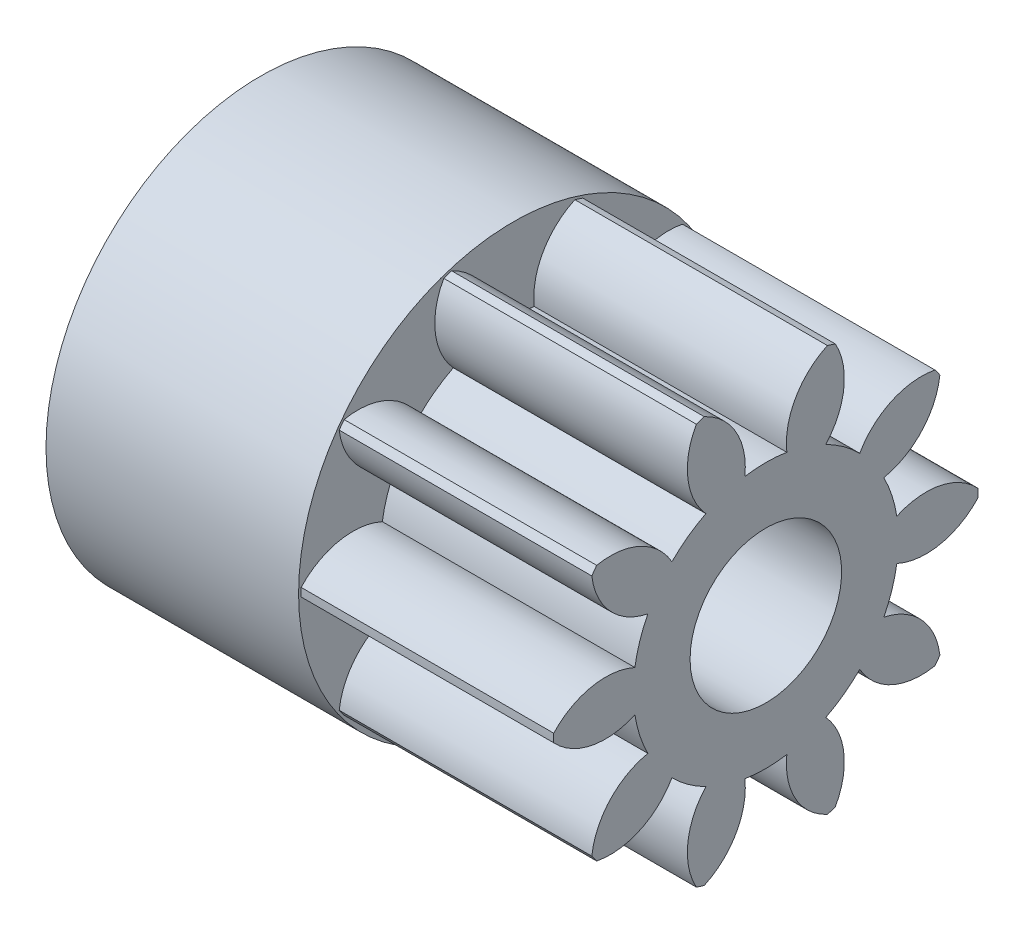
SolidWorks part; units mm, degrees
ref_plane "Plane1" through (0, 0, 0) normal (0, 0, 1) x (1, 0, 0)
ref_plane "Plane2" through (0, 0, 0) normal (0, 1, 0) x (1, 0, 0)
ref_plane "Plane3" through (0, 0, 0) normal (1, 0, 0) x (0, 0, -1)
sketch "HoldingSke" plane through (0, 0, 0) normal (0, 1, 0) x (1, 0, 0)
  line L0 (0, 0) -> (1.4069, -0.2481)
  line L1 (-15, 0) -> (100, 0) construction
  line L2 (0, 0) -> (-2.1039, 2.3779)
  line L3 (0, 0) -> (-11.863, 4.5341)
  line L4 (0, 0) -> (8.5048, 1.4996)
  line L5 (0, 0) -> (-46.8476, -17.4728)
  line L6 (0, 0) -> (-4.1448, -2.7965)
  line L7 (-2.1039, 2.3779) -> (8.6586, 51.2059)
  line L8 (-76.2, 54.61) -> (-75.7, 54.61)
  line L9 (-71.009, 38.7566) -> (-53.1078, 45.2721)
  line L10 (-76.2, 71.12) -> (104.1128, 71.12)
  line L11 (0, 0) -> (-5, 0)
  line L12 (-76.2, 101.6) -> (-76.173, 101.6)
  line L13 (24.9733, 27.94) -> (52.9518, 28.4284)
  line L14 (24.9733, 27.94) -> (24.9743, 27.94)
  line L15 (24.9733, 27.94) -> (100.4006, 29.5858)
  line L16 (-63.627, -0.7) -> (-12.827, -0.7)
  circle A0 centre (0, 0) radius 1.5
  circle A1 centre (0, 0) radius 2.624
  circle A2 centre (0, 0) radius 37.5
  circle A3 centre (0, 0) radius 1.5
  dimension "MHD" = 5.248
  dimension "Hub_dia" = 75
  dimension "Bore" = 3
  dimension "MBD" = 3
  dimension "Num_teeth" = 10
  dimension "Pitch" = 1.4286
  dimension "Overall_len" = 50
  dimension "Show_teeth" = 10
  dimension "Thickness" = 5
  dimension "OAL" = 50.0001
  dimension "T_dim" = 0.5
  dimension "Ap" = 20
  dimension "H" = 19.05
  dimension "Pitch_radius" = 180.3128
  dimension "Width" = 5
  dimension "Backlash" = 0.027
  dimension "Addendum_fac" = 1
  dimension "Dedendum_fac" = 1.25
  dimension "Clearance_fac" = 0.25
  dimension "Dedendum_add" = 0.001
  dimension "Module" = 0.7
sketch "BasProSke" plane through (0, 0, 0) normal (0, 1, 0) x (1, 0, 0)
  line L0 (-10, 0) -> (60, 0) construction
  line L1 (0, 0) -> (0, 4.2)
  line L2 (0, 0) -> (5, 0)
  line L3 (5, 0) -> (5, 4.2)
  line L4 (5, 4.2) -> (0, 4.2)
  dimension "Thickness" = 5
  dimension "Diameter" = 8.4
revolve "Base-Revolve" add sketch "BasProSke" angle 360 about L0
sketch "TooCutSke" plane through (0, 0, 0) normal (1, 0, 0) x (0, 0, -1)
  line L1 (0, 0) -> (0, 107) construction
  line L2 (0, 0) -> (-0.5947, 3.4491) construction
  line L3 (0, 0) -> (-2.1409, 6.589) construction
  line L4 (-0.5947, 3.4491) -> (-1.0705, 3.2945) construction
  arc A0 (0.4155, 2.5909) -> (-0.4155, 2.5909) centre (0, 0) ccw
  arc A1 (1.2546, 4.0349) -> (-1.2546, 4.0349) centre (0, 0) ccw
  circle A2 centre (0, 0) radius 3.5 construction
  circle A3 centre (0, 0) radius 3.2889 construction
  arc A4 (-0.4155, 2.5909) -> (-1.2546, 4.0349) centre (-1.8066, 2.7483) ccw
  arc A5 (1.2546, 4.0349) -> (0.4155, 2.5909) centre (1.8066, 2.7483) ccw
  dimension "Root_dia" = 5.248
  dimension "Overcut_dia" = 8.4508
  dimension "Pitch_dia" = 7
  dimension "Base_dia" = 6.5778
  dimension "Flank_rad" = 1.4
  dimension "Half_ang" = 18
  dimension "Half_CT" = 0.5003
extrude "ToothCut" cut sketch "TooCutSke" along normal through all
fillet "Breaks" [suppressed] radius 0.014
fillet "RootFillets" [suppressed] radius 0.176
pattern_circular "TeethCuts" count 10 every 36 about axis through (-10, 0, 0) along (1, 0, 0) of "ToothCut", "RootFillets", "Breaks"
sketch "HubNeaOneSke" plane through (0, 0, 0) normal (-1, 0, 0) x (0, 0, 1)
  circle A0 centre (0, 0) radius 2.624
  dimension "Diameter" = 5.248
extrude "HubNearOne" [suppressed] add sketch "HubNeaOneSke" along normal blind 45.0001
sketch "HubNeaBotSke" plane through (0, 0, 0) normal (-1, 0, 0) x (0, 0, 1)
  circle A0 centre (0, 0) radius 2.624
  dimension "Diameter" = 5.248
extrude "HubNearBoth" [suppressed] add sketch "HubNeaBotSke" along normal blind 22.5
ref_plane "FarPln" through (5, 0, 0) normal (1, 0, 0) x (0, 0, -1)
sketch "HubFarSke" plane through (5, 0, 0) normal (1, 0, 0) x (0, 0, -1)
  circle A0 centre (0, 0) radius 2.624
  dimension "Diameter" = 5.248
extrude "HubFar" [suppressed] add sketch "HubFarSke" along normal blind 22.5
sketch "BorSke" plane through (0, 0, 0) normal (1, 0, 0) x (0, 0, -1)
  circle A0 centre (0, 0) radius 1.5
  dimension "Diameter" = 3
extrude "Bore" cut sketch "BorSke" along normal mid plane 100.0001
sketch "KeySke" plane through (0, 0, 0) normal (1, 0, 0) x (0, 0, -1)
  line L0 (-0.6, 0) -> (-0.6, 2)
  line L1 (-0.6, 2) -> (0.6, 2)
  line L2 (0.6, 2) -> (0.6, 0)
  line L3 (0, 0) -> (0, 34) construction
  line L4 (-0.6, 0) -> (0.6, 0)
  dimension "Offset" = 2
  dimension "Width" = 1.2
extrude "Keyway" [suppressed] cut sketch "KeySke" along normal mid plane 100.0001
pattern_circular "Keyway2" [suppressed] count 2 every 90 about axis through (-10, 0, 0) along (1, 0, 0)
sketch "Croquis1" plane through (0, 0, 0) normal (-1, 0, 0) x (0, 0, 1)
  circle A0 centre (0, 0) radius 4.25
  circle A1 centre (0, 0) radius 3.25
  dimension "D1" = 8.5
  dimension "D2" = 6.5
extrude "Saliente-Extruir1" add sketch "Croquis1" along normal blind 5
sketch "Croquis2" plane through (0, 0, 0) normal (-1, 0, 0) x (0, 0, 1)
  circle A0 centre (0, 0) radius 3.25
  circle A1 centre (0, 0) radius 3.25 construction
extrude "Saliente-Extruir2" add sketch "Croquis2" along normal blind 2
sketch "Croquis3" plane through (-2, 0, 0) normal (-1, 0, 0) x (0, 0, 1)
  line L0 (-1.5, 2.8831) -> (-1.5, -2.8831)
  circle A0 centre (0, 0) radius 3.25 construction
  circle A1 centre (0, 0) radius 3.25 construction
  arc A2 (-1.5, 2.8831) -> (-1.5, -2.8831) centre (0, 0) ccw
  dimension "D1" = 1.5
extrude "Saliente-Extruir3" add sketch "Croquis3" along normal blind 2
equation "' \"Module@HoldingSke\" = 6.35"
equation "' \"Num_teeth@HoldingSke\" = 12"
equation "' \"Ap@HoldingSke\" =  20"
equation "' \"Ap@HoldingSke\" = 20"
equation "' \"Width@HoldingSke\" = 0.5 * 25.4"
equation "' \"Hub_dia@HoldingSke\"= 1 * 25.4"
equation "' \"Hub_dia@HoldingSke\" = 1 * 25.4"
equation "' \"Overall_len@HoldingSke\" = 1.0 * 25.4"
equation "' \"Bore@HoldingSke\" = 0.75 * 25.4"
equation "' \"T_dim@HoldingSke\" = 0.1 * 25.4"
equation "' \"Width@KeySke\" = 0.25 * 25.4"
equation "' \"Show_teeth@HoldingSke\" = 13"
equation "' \"Backlash@HoldingSke\" = 0.009 * 25.4"
equation "' \"Addendum_fac@HoldingSke\" = 1.0"
equation "' \"Dedendum_fac@HoldingSke\" = 1.25"
equation "' \"Dedendum_add@HoldingSke\" = 0.00005 * 25.4"
equation "' \"Clearance_fac@HoldingSke\" = 0.25"
equation "\"Pitch@HoldingSke\" = 1 / \"Module@HoldingSke\""
equation "\"Overcut_dia@TooCutSke\" = (\"Num_teeth@HoldingSke\" + 2 * \"Addendum_fac@HoldingSke\") / \"Pitch@HoldingSke\" + 0.002 * 25.4"
equation "\"Pitch_dia@TooCutSke\" = \"Num_teeth@HoldingSke\" / \"Pitch@HoldingSke\""
equation "\"Base_dia@TooCutSke\" = \"Num_teeth@HoldingSke\" / \"Pitch@HoldingSke\" * cos((\"Ap@HoldingSke\"  * 3.14159265 / 180))"
equation "\"Root_dia@TooCutSke\" = (\"Num_teeth@HoldingSke\" + 2) / \"Pitch@HoldingSke\" - 2 * (\"Addendum_fac@HoldingSke\" + \"Dedendum_fac@HoldingSke\") / \"Pitch@HoldingSke\" - \"Dedendum_add@HoldingSke\" * 2"
equation "\"Half_ang@TooCutSke\" = 180 / \"Num_teeth@HoldingSke\""
equation "\"Half_CT@TooCutSke\" = \"Num_teeth@HoldingSke\" / \"Pitch@HoldingSke\" * sin((3.14159265 / 2 / \"Num_teeth@HoldingSke\")) / 2 - 7 * \"Backlash@HoldingSke\" / 4"
equation "\"Flank_rad@TooCutSke\" = \"Num_teeth@HoldingSke\" / \"Pitch@HoldingSke\" / 5"
equation "\"Radius@RootFillets\" = \"Clearance_fac@HoldingSke\" / \"Pitch@HoldingSke\" + \"Dedendum_add@HoldingSke\""
equation "\"Break_rad@Breaks\" = 0.02 / \"Pitch@HoldingSke\""
equation "\"Thickness@HoldingSke\" = \"Width@HoldingSke\""
equation "\"OAL@HoldingSke\" = \"Thickness@HoldingSke\""
equation "\"MHD@HoldingSke\" = (\"Num_teeth@HoldingSke\" + 2) / \"Pitch@HoldingSke\" - 2 * (\"Addendum_fac@HoldingSke\" + \"Dedendum_fac@HoldingSke\")  / \"Pitch@HoldingSke\" - \"Dedendum_add@HoldingSke\" * 2"
equation "\"MBD@HoldingSke\" = (\"Num_teeth@HoldingSke\" + 2) / \"Pitch@HoldingSke\" - 2 * (\"Addendum_fac@HoldingSke\" + \"Dedendum_fac@HoldingSke\")  / \"Pitch@HoldingSke\" - \"Dedendum_add@HoldingSke\" * 2 - 0.002 * 25.4"
equation "\"MHD@HoldingSke\" = ((sgn( \"MHD@HoldingSke\" - \"Hub_dia@HoldingSke\" )-1)*( \"MHD@HoldingSke\" - \"Hub_dia@HoldingSke\" ))/-2+ \"Hub_dia@HoldingSke\""
equation "\"MBD@HoldingSke\" = ((sgn( \"MBD@HoldingSke\" - \"Bore@HoldingSke\" )-1)*( \"MBD@HoldingSke\" - \"Bore@HoldingSke\" ))/-2+ \"Bore@HoldingSke\""
equation "\"OAL@HoldingSke\" = ((sgn( \"OAL@HoldingSke\" - \"Overall_len@HoldingSke\" )+1)*( \"OAL@HoldingSke\" - \"Overall_len@HoldingSke\" ))/2 + \"Overall_len@HoldingSke\" + 0.000002 * 25.4"
equation "\"Num_teeth@TeethCuts\" = int( \"Show_teeth@HoldingSke\" ) + 1"
equation "\"Num_teeth@TeethCuts\" = ((sgn( \"Num_teeth@TeethCuts\" - \"Num_teeth@HoldingSke\" )-1)*( \"Num_teeth@TeethCuts\" - \"Num_teeth@HoldingSke\" ))/-2+ \"Num_teeth@HoldingSke\""
equation "\"Num_teeth@TeethCuts\" = ((sgn( \"Num_teeth@TeethCuts\" - 2.0)+1)*( \"Num_teeth@TeethCuts\" - 2.0))/2 +2.0"
equation "\"Angle@TeethCuts\" = 360.0 / \"Num_teeth@HoldingSke\""
equation "\"Diameter@BasProSke\" = (\"Num_teeth@HoldingSke\" + 2 * \"Addendum_fac@HoldingSke\") / \"Pitch@HoldingSke\""
equation "\"Thickness@BasProSke\"  = \"Thickness@HoldingSke\""
equation "' \"Fillet_rad@BasProSke\" =  \"Thickness@HoldingSke\" * 0.05"
equation "' \"Fillet_rad@BasProSke\" = \"Thickness@HoldingSke\" * 0.05"
equation "\"MHD@HoldingSke\" = ((sgn( \"MHD@HoldingSke\" - \"Root_dia@TooCutSke\" )-1)*( \"MHD@HoldingSke\" - \"Root_dia@TooCutSke\" ))/-2+ \"Root_dia@TooCutSke\""
equation "\"Diameter@HubNeaOneSke\" = \"MHD@HoldingSke\""
equation "\"Length@HubNearOne\" = \"OAL@HoldingSke\" - \"Thickness@BasProSke\""
equation "\"Diameter@HubNeaBotSke\" = \"MHD@HoldingSke\""
equation "\"Length@HubNearBoth\" = ( \"OAL@HoldingSke\" - \"Thickness@BasProSke\" ) / 2.0"
equation "\"Thickness@FarPln\" = \"Thickness@BasProSke\""
equation "\"Diameter@HubFarSke\" = \"MHD@HoldingSke\""
equation "\"Length@HubFar\" = ( \"OAL@HoldingSke\" - \"Thickness@BasProSke\" ) / 2.0"
equation "\"Diameter@BorSke\" = \"MBD@HoldingSke\""
equation "\"D1@Bore\" = \"OAL@HoldingSke\" * 2.0"
equation "\"D1@Keyway\" = \"OAL@HoldingSke\" * 2.0"
equation "\"Offset@KeySke\" = \"T_dim@HoldingSke\" + \"MBD@HoldingSke\" / 2.0"
